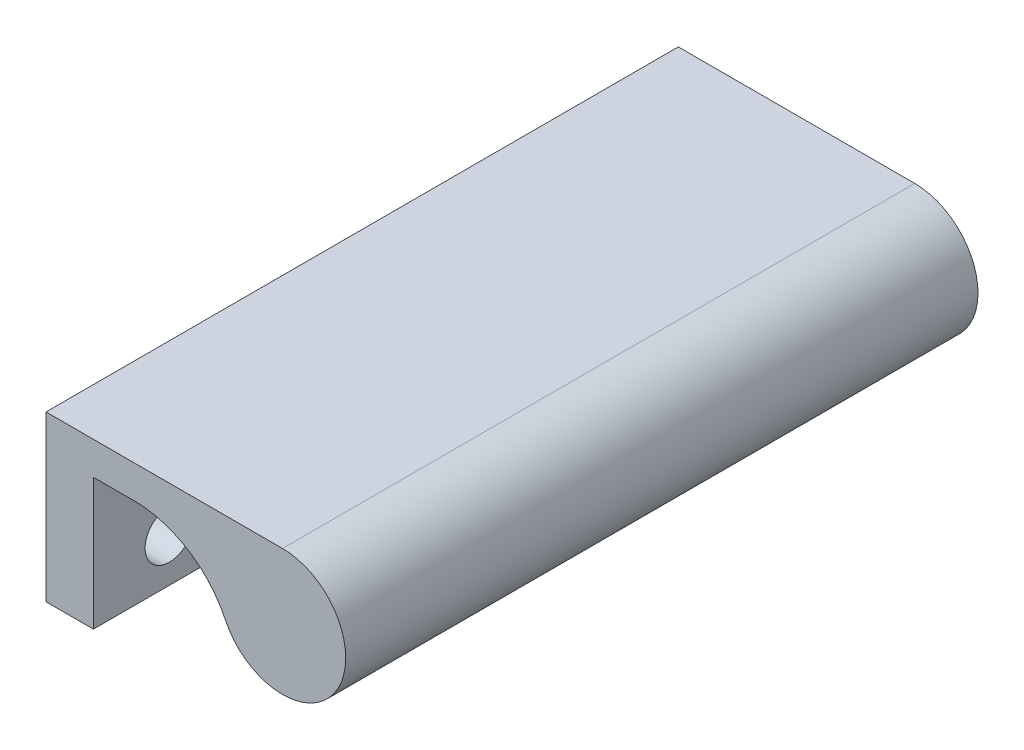
SolidWorks part; units mm, degrees
ref_plane "Front Plane" through (0, 0, 0) normal (1, 0, 0) x (0, 1, 0)
ref_plane "Top Plane" through (0, 0, 0) normal (0, 0, 1) x (0, 1, 0)
ref_plane "Right Plane" through (0, 0, 0) normal (0, 1, 0) x (-1, 0, 0)
ref_plane "Plane1"
sketch "Sketch1" plane through (0, 0, 0) normal (1, 0, 0) x (0, 1, 0)
  line L0 (0, -63.5) -> (16.51, -63.5)
  line L1 (16.51, -63.5) -> (16.51, 0)
  line L2 (16.51, 0) -> (0, 0)
  line L3 (0, 0) -> (0, -63.5)
  circle A0 centre (4.445, -7.62) radius 2.4329
  circle A1 centre (4.445, -15.6185) radius 2.4329
  circle A2 centre (4.445, -23.6169) radius 2.4329
  circle A3 centre (4.445, -31.6154) radius 2.4329
  circle A4 centre (4.445, -39.6138) radius 2.4329
  circle A5 centre (4.445, -47.6123) radius 2.4329
  circle A6 centre (4.445, -55.6108) radius 2.4329
  dimension "D1" = 63.5
  dimension "D2" = 16.51
  dimension "D3" = 7.9985
  dimension "D4" = 31.6154
extrude "Extrusion1" add sketch "Sketch1" along normal blind 4.7625 contours L2 L3 L0 L1 A6 A5 A4 A3 A2 A1 A0
sketch "Sketch2" plane through (4.7625, 0, 0) normal (1, 0, 0) x (0, 0, -1)
  line L0 (0, 13.208) -> (63.5, 13.208)
  line L1 (63.5, 13.208) -> (63.5, 16.51)
  line L2 (63.5, 16.51) -> (0, 16.51)
  line L3 (0, 16.51) -> (0, 13.208)
  dimension "D1" = 3.302
extrude "Extrusion2" add sketch "Sketch2" along normal blind 1.016
sketch "Sketch3" plane through (0, 0, 0) normal (0, 0, 1) x (1, 0, 0)
  line L0 (23.749, 16.51) -> (5.7785, 16.51)
  line L1 (5.7785, 16.51) -> (5.7785, 13.208)
  line L2 (5.7785, 13.208) -> (8.8494, 13.208)
  arc A0 (18.0184, 7.4246) -> (8.8494, 13.208) centre (8.8494, 3.048) ccw
  arc A1 (18.0184, 7.4246) -> (23.749, 16.51) centre (23.749, 10.16) ccw
  dimension "D1" = 12.7
extrude "Extrusion3" add sketch "Sketch3" against normal blind 63.5
